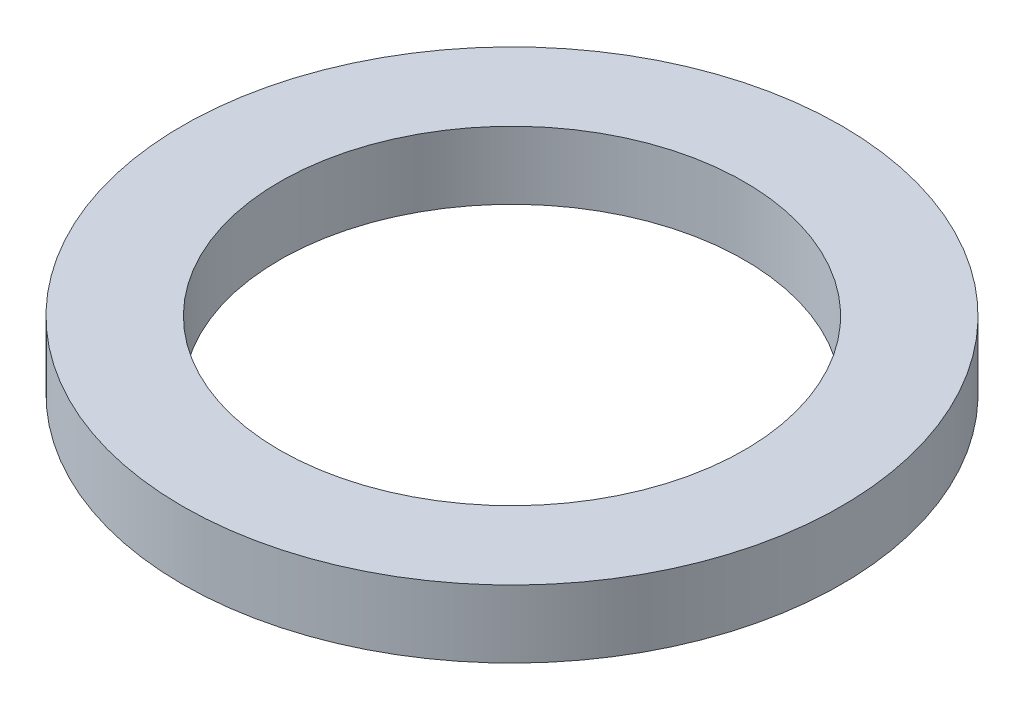
SolidWorks part; units mm, degrees
ref_plane "Front Plane" through (0, 0, 0) normal (0, 0, 1) x (1, 0, 0)
ref_plane "Top Plane" through (0, 0, 0) normal (0, 1, 0) x (1, 0, 0)
ref_plane "Right Plane" through (0, 0, 0) normal (1, 0, 0) x (0, 0, -1)
sketch "Sketch1" plane through (0, 0, 0) normal (0, 1, 0) x (1, 0, 0)
  circle A0 centre (0, 0) radius 3.9
  dimension "D1" = 7.8
extrude "Boss-Extrude1" add sketch "Sketch1" along normal blind 0.8
sketch "Sketch2" plane through (0, 0.8, 0) normal (0, 1, 0) x (1, 0, 0)
  circle A0 centre (0, 0) radius 2.75
  dimension "D1" = 5.5
extrude "Cut-Extrude1" cut sketch "Sketch2" against normal through all
